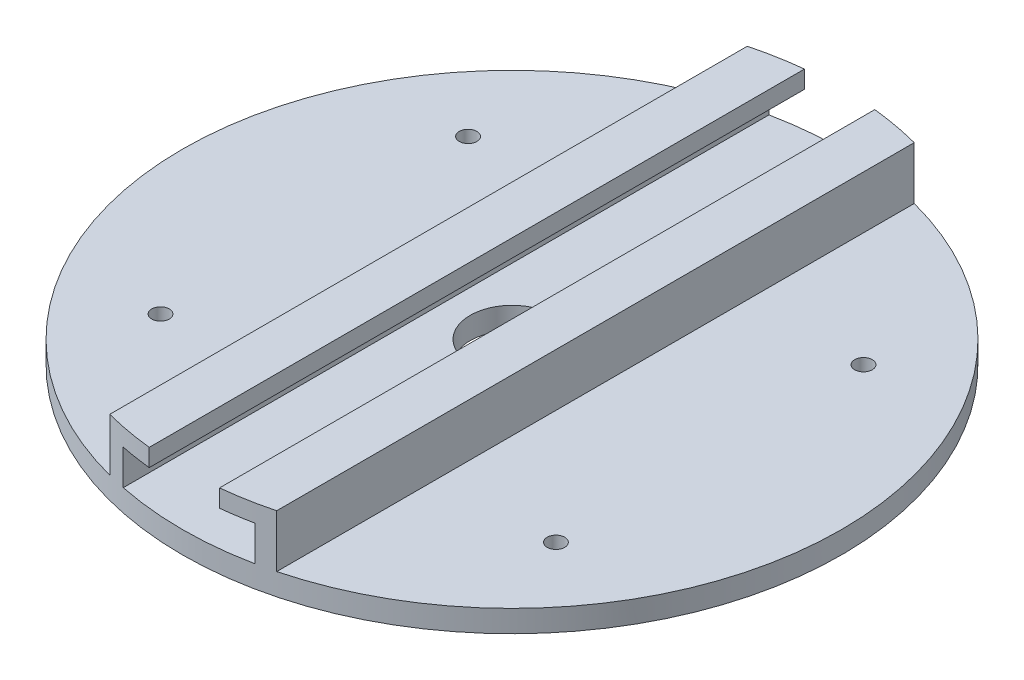
SolidWorks part; units mm, degrees
ref_plane "Front" through (0, 0, 0) normal (0, 0, 1) x (1, 0, 0)
ref_plane "Top" through (0, 0, 0) normal (0, 1, 0) x (1, 0, 0)
ref_plane "Right" through (0, 0, 0) normal (1, 0, 0) x (0, 0, -1)
sketch "Sketch1" plane through (0, 0, 0) normal (0, 1, 0) x (1, 0, 0)
  circle A0 centre (0, 0) radius 75
  dimension "D1" = 150
extrude "Boss-Extrude1" add sketch "Sketch1" along normal blind 5
sketch "Sketch2" plane through (0, 0, 0) normal (0, 0, 1) x (1, 0, 0)
  line L0 (75, 5) -> (-75, 5) construction
  line L1 (-15, 13) -> (15, 13)
  line L2 (-15, 13) -> (-15, 5)
  line L3 (-15, 5) -> (15, 5)
  line L4 (15, 13) -> (15, 5)
  line L5 (-15, 13) -> (15, 5) construction
  line L6 (-15, 5) -> (15, 13) construction
  line L7 (-8, 13) -> (-8, 17)
  line L8 (-8, 17) -> (-19, 17)
  line L9 (-19, 17) -> (-19, 5)
  line L10 (-19, 5) -> (-15, 5)
  line L11 (19, 5) -> (19, 17)
  line L12 (19, 17) -> (8, 17)
  line L13 (8, 17) -> (8, 13)
  line L14 (15, 5) -> (19, 5)
  point P0 (0, 9)
  dimension "D1" = 30
  dimension "D2" = 8
  dimension "D3" = 4
  dimension "D5" = 16
extrude "Boss-Extrude2" add sketch "Sketch2" along normal up to surface and the other way up to surface contours L9 L10 L2 L1 L7 L8 | L4 L14 L11 L12 L13 L1 up to face at (0, 5, 75) other way up to face at (0, 5, 75)
sketch "Sketch3" plane through (0, 5, 0) normal (0, 1, 0) x (1, 0, 0)
  circle A0 centre (0, 0) radius 9.5
  dimension "D1" = 19
extrude "Cut-Extrude1" cut sketch "Sketch3" against normal through all
sketch "Sketch4" plane through (0, 5, 0) normal (0, 1, 0) x (1, 0, 0)
  line L1 (-45, -35) -> (45, -35) construction
  line L2 (-45, -35) -> (-45, 35) construction
  line L3 (-45, 35) -> (45, 35) construction
  line L4 (45, -35) -> (45, 35) construction
  line L5 (-45, -35) -> (45, 35) construction
  line L6 (-45, 35) -> (45, -35) construction
  circle A0 centre (-45, 35) radius 2
  circle A1 centre (45, 35) radius 2
  circle A2 centre (45, -35) radius 2
  circle A3 centre (-45, -35) radius 2
  point P0 (0, 0)
  dimension "D3" = 4
  dimension "D1" = 70
  dimension "D2" = 90
extrude "Cut-Extrude2" cut sketch "Sketch4" against normal through all
